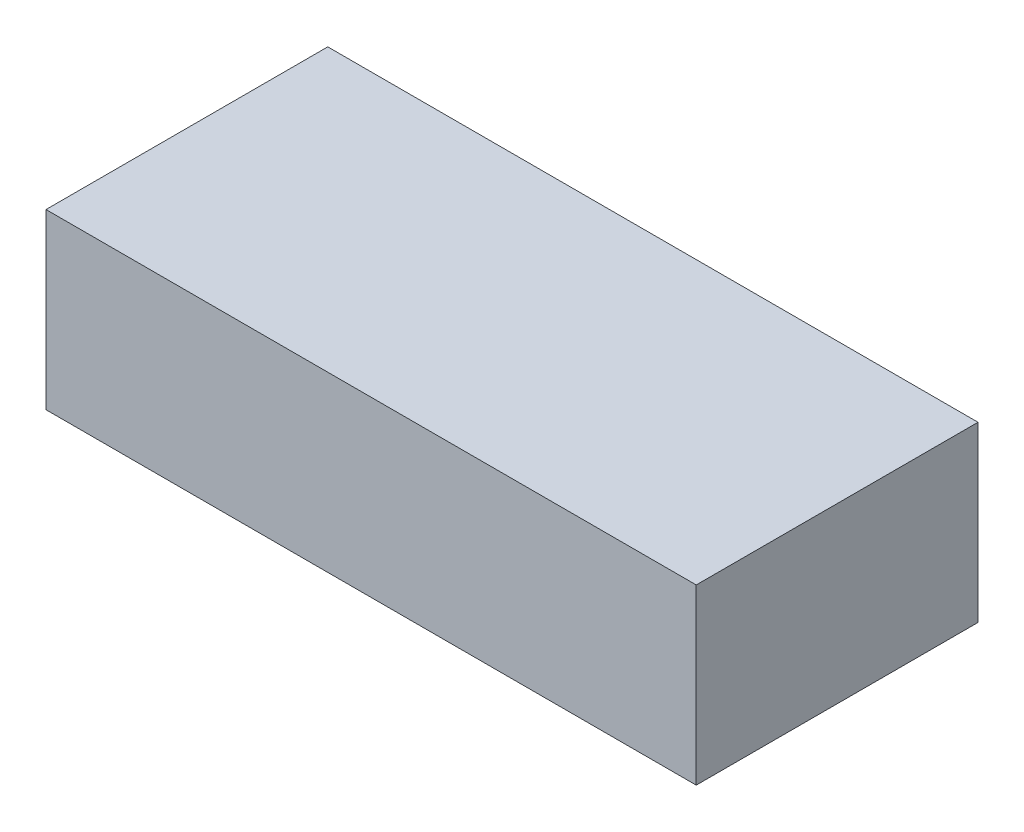
SolidWorks part; units mm, degrees
ref_plane "Front Plane" through (0, 0, 0) normal (0, 0, 1) x (1, 0, 0)
ref_plane "Top Plane" through (0, 0, 0) normal (0, 1, 0) x (1, 0, 0)
ref_plane "Right Plane" through (0, 0, 0) normal (1, 0, 0) x (0, 0, -1)
sketch "Sketch1" plane through (0, 0, 0) normal (0, 1, 0) x (1, 0, 0)
  line L1 (-75, -32.5) -> (75, -32.5)
  line L2 (-75, -32.5) -> (-75, 32.5)
  line L3 (-75, 32.5) -> (75, 32.5)
  line L4 (75, -32.5) -> (75, 32.5)
  line L5 (-75, -32.5) -> (75, 32.5) construction
  line L6 (-75, 32.5) -> (75, -32.5) construction
  point P0 (0, 0)
  dimension "D1" = 150
  dimension "D2" = 65
extrude "Boss-Extrude1" add sketch "Sketch1" along normal blind 40
sketch "Sketch2" plane through (0, 0, 0) normal (0, -1, 0) x (1, 0, 0)
  line L0 (-75, 32.5) -> (75, 32.5) construction
  line L1 (-71.952, -29.452) -> (71.952, -29.452)
  line L2 (-71.952, -29.452) -> (-71.952, 29.452)
  line L3 (-71.952, 29.452) -> (71.952, 29.452)
  line L4 (71.952, -29.452) -> (71.952, 29.452)
  line L5 (-71.952, -29.452) -> (71.952, 29.452) construction
  line L6 (-71.952, 29.452) -> (71.952, -29.452) construction
  line L7 (-75, -32.5) -> (-75, 32.5) construction
  point P0 (0, 0)
  dimension "D1" = 3.048
  dimension "D2" = 3.048
extrude "Cut-Extrude1" cut sketch "Sketch2" against normal blind 28.4
sketch "Sketch3" plane through (0, 0, -32.5) normal (0, 0, -1) x (-1, 0, 0)
  line L1 (75, 40) -> (75, 0) construction
  line L2 (-75, 0) -> (75, 0) construction
  circle A0 centre (38.12, 12.19) radius 4.33
  dimension "D3" = 8.66
  dimension "D1" = 36.88
  dimension "D2" = 12.19
extrude "Cut-Extrude2" cut sketch "Sketch3" against normal up to surface (3.048 mm away) up to face at (0, 14.2, -29.452)
